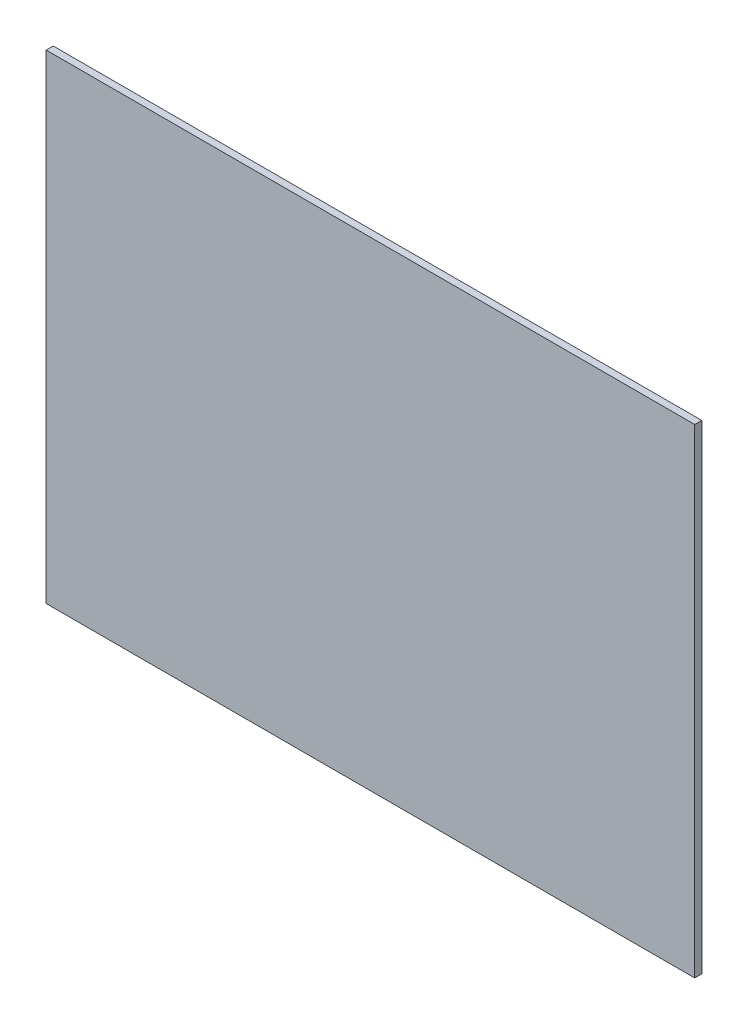
SolidWorks part; units mm, degrees
ref_plane "Front Plane" through (0, 0, 0) normal (0, 0, 1) x (1, 0, 0)
ref_plane "Top Plane" through (0, 0, 0) normal (0, 1, 0) x (1, 0, 0)
ref_plane "Right Plane" through (0, 0, 0) normal (1, 0, 0) x (0, 0, -1)
sketch "Sketch1" plane through (0, 0, 0) normal (0, 0, 1) x (1, 0, 0)
  line L1 (-292.1, 215.9) -> (292.1, 215.9)
  line L2 (-292.1, 215.9) -> (-292.1, -215.9)
  line L3 (-292.1, -215.9) -> (292.1, -215.9)
  line L4 (292.1, 215.9) -> (292.1, -215.9)
  line L5 (-292.1, 215.9) -> (292.1, -215.9) construction
  line L6 (-292.1, -215.9) -> (292.1, 215.9) construction
  point P0 (0, 0)
  dimension "D1" = 584.2
  dimension "D2" = 431.8
extrude "Boss-Extrude1" add sketch "Sketch1" along normal blind 6.35
